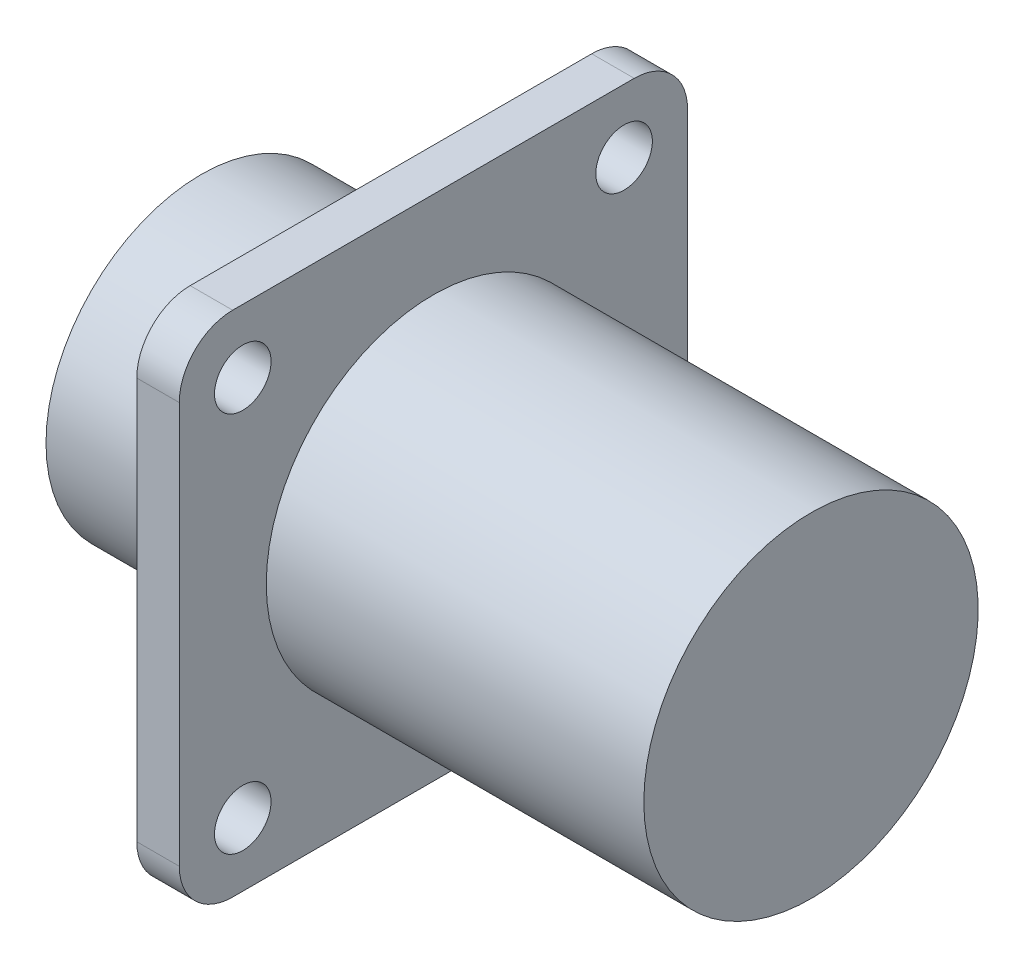
SolidWorks part; units mm, degrees
ref_plane "Front Plane" through (0, 0, 0) normal (0, 0, 1) x (1, 0, 0)
ref_plane "Top Plane" through (0, 0, 0) normal (0, 1, 0) x (1, 0, 0)
ref_plane "Right Plane" through (0, 0, 0) normal (1, 0, 0) x (0, 0, -1)
sketch "Sketch1" plane through (0, 0, 0) normal (0, 0, 1) x (1, 0, 0)
  line L0 (0, 0) -> (67.6328, 0) construction
  line L1 (0, 0) -> (0, 8.725)
  line L2 (0, 8.725) -> (10.67, 8.725)
  line L3 (10.67, 8.725) -> (10.67, 30)
  line L4 (10.67, 30) -> (13.06, 30)
  line L5 (13.06, 30) -> (13.06, 9.4)
  line L6 (13.06, 9.4) -> (34.29, 9.4)
  line L7 (34.29, 9.4) -> (34.29, 0)
  line L8 (34.29, 0) -> (0, 0)
  dimension "D1" = 2.39
  dimension "D2" = 10.67
  dimension "D3" = 34.29
  dimension "D4" = 17.45
  dimension "D5" = 18.8
  dimension "D6" = 60
revolve "Revolve1" add sketch "Sketch1" angle 360 about L0
sketch "Sketch2" plane through (10.67, 0, 0) normal (-1, 0, 0) x (0, 0, 1)
  line L0 (-14.29, 14.29) -> (14.29, -14.29) construction
  line L1 (-11.29, 14.29) -> (11.29, 14.29)
  line L2 (-14.29, 11.29) -> (-14.29, -11.29)
  line L3 (-11.29, -14.29) -> (11.29, -14.29)
  line L4 (14.29, 11.29) -> (14.29, -11.29)
  line L5 (-10.72, -10.72) -> (10.72, 10.72) construction
  circle A0 centre (10.72, 10.72) radius 1.59
  circle A1 centre (-10.72, 10.72) radius 1.59
  circle A2 centre (-10.72, -10.72) radius 1.59
  circle A3 centre (10.72, -10.72) radius 1.59
  arc A4 (-14.29, -11.29) -> (-11.29, -14.29) centre (-11.29, -11.29) ccw
  arc A5 (11.29, -14.29) -> (14.29, -11.29) centre (11.29, -11.29) ccw
  arc A6 (11.29, 14.29) -> (14.29, 11.29) centre (11.29, 11.29) cw
  arc A7 (-11.29, 14.29) -> (-14.29, 11.29) centre (-11.29, 11.29) ccw
  point P20 (14.29, 14.29)
  dimension "D4" = 3.18
  dimension "D5" = 3
  dimension "D1" = 28.58
  dimension "D2" = 21.44
  dimension "D3" = 21.44
extrude "Cut-Extrude1" cut sketch "Sketch2" against normal through all flip side to cut
